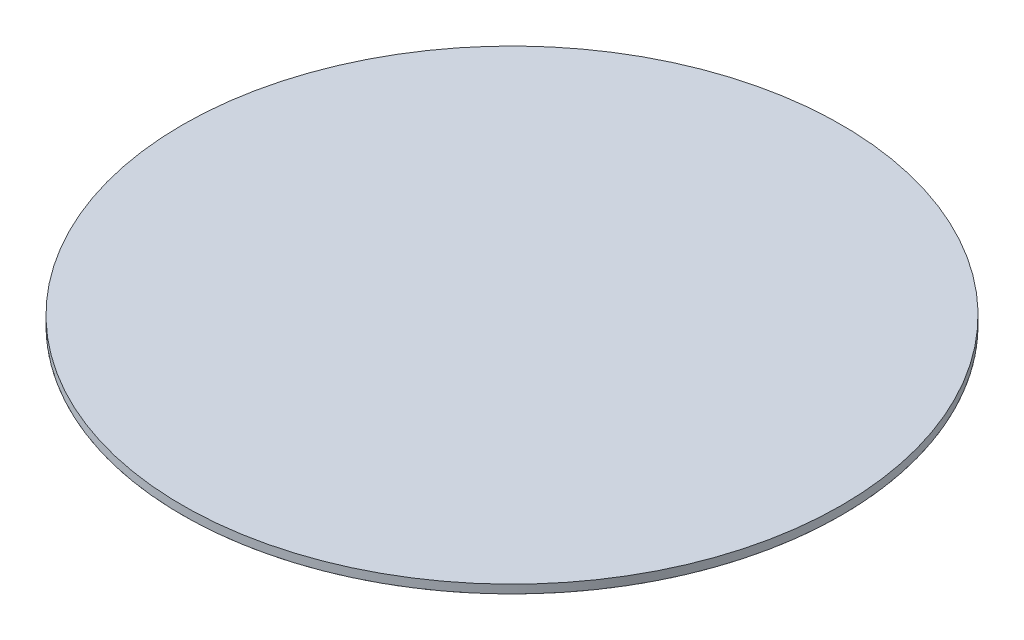
SolidWorks part; units mm, degrees
material "Oak"
ref_plane "Front Plane" through (0, 0, 0) normal (0, 0, 1) x (1, 0, 0)
ref_plane "Top Plane" through (0, 0, 0) normal (0, 1, 0) x (1, 0, 0)
ref_plane "Right Plane" through (0, 0, 0) normal (1, 0, 0) x (0, 0, -1)
sketch "Sketch2" plane through (0, 0, 0) normal (1, 0, 0) x (0, 0, -1)
  line L0 (0, 0) -> (0, -10) construction
  line L1 (0, 0) -> (194, 0) construction
  line L2 (194, 0) -> (174, 0)
  line L3 (69.7148, -10) -> (-69.7148, -10) construction
  spline S0 degree 3 poles (0, -10) (100, -10) (140.6667, 0) (174, 0) knots 0 0 0 0 1 1 1 1
  dimension "D3" = 300
  dimension "D4" = 100
  dimension "D1" = 194
  dimension "D2" = 20
surface "Surface-Revolve1" sketch "Sketch2" parameters "D1"=360
ref_plane "Plane2" through (0, 0, 0) normal (0, 1, 0) x (1, 0, 0)
sketch "Sketch4" plane through (0, 0, 0) normal (0, 1, 0) x (1, 0, 0)
  circle A0 centre (0, 0) radius 194
extrude "Boss-Extrude2" add sketch "Sketch4" along normal blind 5
